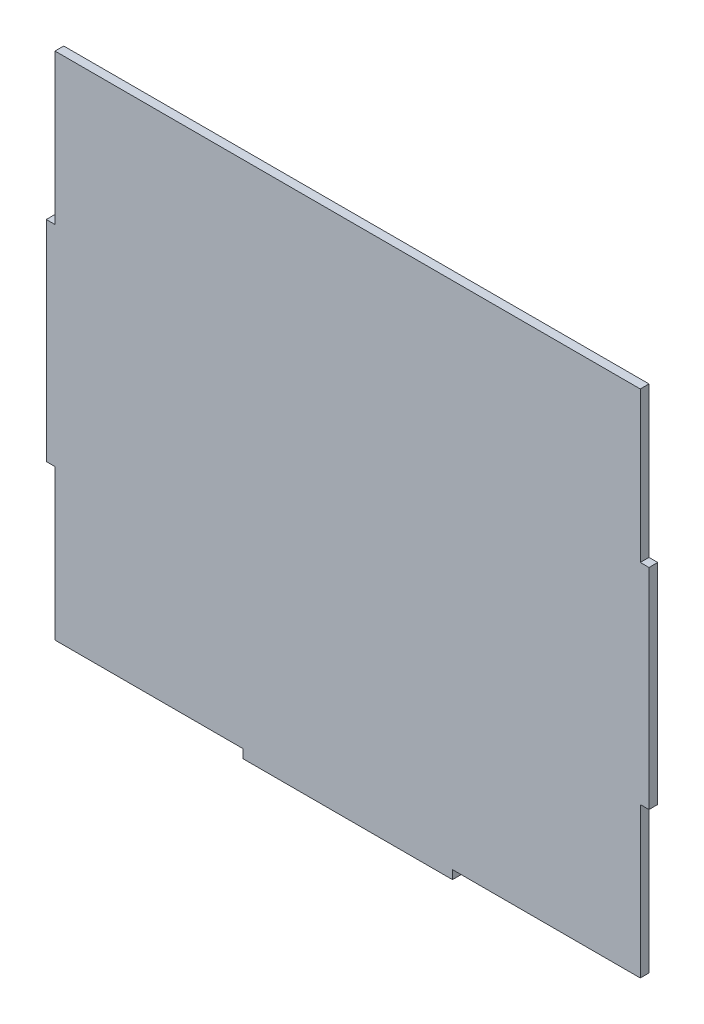
SolidWorks part; units mm, degrees
ref_plane "Front Plane" through (0, 0, 0) normal (0, 0, 1) x (1, 0, 0)
ref_plane "Top Plane" through (0, 0, 0) normal (0, 1, 0) x (1, 0, 0)
ref_plane "Right Plane" through (0, 0, 0) normal (1, 0, 0) x (0, 0, -1)
sketch "Sketch1" plane through (0, 0, 0) normal (0, 0, 1) x (1, 0, 0)
  line L1 (-106.3625, 92.71) -> (106.3625, 92.71)
  line L2 (-106.3625, 92.71) -> (-106.3625, -92.71)
  line L3 (-106.3625, -92.71) -> (106.3625, -92.71)
  line L4 (106.3625, 92.71) -> (106.3625, -92.71)
  line L5 (-106.3625, 92.71) -> (106.3625, -92.71) construction
  line L6 (-106.3625, -92.71) -> (106.3625, 92.71) construction
  point P0 (0, 0)
  dimension "D1" = 185.42
  dimension "D2" = 212.725
extrude "Boss-Extrude1" add sketch "Sketch1" along normal blind 3.175
sketch "Sketch2" plane through (0, 0, 3.175) normal (0, 0, 1) x (1, 0, 0)
  line L0 (-106.3625, 0) -> (-106.3625, 92.71) construction
  line L1 (-103.1875, -46.355) -> (-106.3625, -46.355) construction
  line L2 (-103.1875, -71.755) -> (-103.1875, -20.955)
  line L3 (-106.3625, 92.71) -> (-106.3625, -92.71) construction
  line L4 (-103.1875, 46.355) -> (-106.3625, 46.355) construction
  line L5 (-106.3625, 71.755) -> (-103.1875, 71.755)
  line L6 (-106.3625, 71.755) -> (-106.3625, 20.955)
  line L7 (-106.3625, 20.955) -> (-103.1875, 20.955)
  line L8 (-103.1875, 71.755) -> (-103.1875, 20.955)
  line L9 (-106.3625, 0) -> (0, 0) construction
  line L10 (-106.3625, -20.955) -> (-103.1875, -20.955)
  line L11 (-106.3625, -71.755) -> (-106.3625, -20.955)
  line L12 (-106.3625, -71.755) -> (-103.1875, -71.755)
  line L13 (0, 0) -> (0, 92.71) construction
  line L14 (106.3625, 92.71) -> (-106.3625, 92.71) construction
  line L15 (103.1875, 46.355) -> (106.3625, 46.355) construction
  line L16 (103.1875, -46.355) -> (106.3625, -46.355) construction
  line L17 (106.3625, -71.755) -> (103.1875, -71.755)
  line L18 (106.3625, -71.755) -> (106.3625, -20.955)
  line L19 (106.3625, -20.955) -> (103.1875, -20.955)
  line L20 (103.1875, 71.755) -> (103.1875, 20.955) construction
  line L21 (106.3625, 20.955) -> (103.1875, 20.955)
  line L22 (106.3625, 71.755) -> (106.3625, 20.955)
  line L23 (106.3625, 71.755) -> (103.1875, 71.755)
  line L24 (103.1875, -71.755) -> (103.1875, -20.955) construction
  line L25 (103.1875, -71.755) -> (100.0125, -71.755)
  line L26 (103.1875, 71.755) -> (100.0125, 71.755)
  line L27 (103.1875, 71.755) -> (103.1875, 20.955) construction
  line L28 (103.1875, 20.955) -> (100.0125, 20.955)
  line L29 (100.0125, 71.755) -> (100.0125, 20.955)
  line L30 (100.0125, -71.755) -> (100.0125, -20.955)
  line L31 (103.1875, -20.955) -> (100.0125, -20.955)
  dimension "D1" = 3.175
  dimension "D2" = 50.8
  dimension "D3" = 6.35
extrude "Cut-Extrude1" [suppressed] cut sketch "Sketch2" against normal through all
sketch "Sketch3" [suppressed] plane through (0, 0, 3.175) normal (0, 0, 1) x (1, 0, 0)
  line L0 (0, 114.3) -> (0, -114.3) construction
  line L1 (112.395, 114.3) -> (-112.395, 114.3) construction
  line L2 (-112.395, -114.3) -> (112.395, -114.3) construction
sketch "Sketch4" plane through (0, 0, 0) normal (0, 0, -1) x (-1, 0, 0)
  line L0 (106.3625, -92.71) -> (-106.3625, -92.71) construction
  line L1 (0, -89.535) -> (0, 92.71) construction
  line L2 (-38.1, -89.535) -> (38.1, -89.535)
  line L3 (-38.1, -89.535) -> (-38.1, -92.71)
  line L4 (-38.1, -92.71) -> (38.1, -92.71)
  line L5 (0, 0) -> (0, -92.71) construction
  line L6 (0, -92.71) -> (-106.3625, -92.71) construction
  line L7 (38.1, -89.535) -> (38.1, -92.71)
  line L9 (-106.3625, 92.71) -> (106.3625, 92.71) construction
  dimension "D1" = 76.2
  dimension "D2" = 3.175
extrude "Cut-Extrude2" [suppressed] cut sketch "Sketch4" against normal through all
sketch "Sketch5" plane through (0, 0, 0) normal (0, 0, -1) x (-1, 0, 0)
  line L0 (-106.3625, 0) -> (0, 0) construction
  line L1 (-106.3625, 38.1) -> (-109.5375, 38.1)
  line L2 (-106.3625, 38.1) -> (-106.3625, -38.1)
  line L3 (-106.3625, -38.1) -> (-109.5375, -38.1)
  line L4 (-109.5375, 38.1) -> (-109.5375, -38.1)
  line L5 (-106.3625, 38.1) -> (-109.5375, -38.1) construction
  line L6 (-106.3625, -38.1) -> (-109.5375, 38.1) construction
  line L7 (-106.3625, -92.71) -> (-106.3625, 92.71) construction
  line L8 (0, 0) -> (0, 92.71) construction
  line L9 (-106.3625, 92.71) -> (106.3625, 92.71) construction
  line L10 (106.3625, -38.1) -> (109.5375, 38.1) construction
  line L11 (106.3625, 38.1) -> (109.5375, -38.1) construction
  line L12 (109.5375, 38.1) -> (109.5375, -38.1)
  line L13 (106.3625, -38.1) -> (109.5375, -38.1)
  line L14 (106.3625, 38.1) -> (106.3625, -38.1)
  line L15 (106.3625, 38.1) -> (109.5375, 38.1)
  point P0 (-107.95, 0)
  point P17 (107.95, 0)
  dimension "D1" = 76.2
  dimension "D2" = 3.175
extrude "Boss-Extrude2" add sketch "Sketch5" against normal up to surface (3.175 mm away) up to face at (0, 0, 3.175)
sketch "Sketch6" plane through (0, 0, 0) normal (0, 0, -1) x (-1, 0, 0)
  line L0 (106.3625, -92.71) -> (-106.3625, -92.71) construction
  line L1 (0, 8.89) -> (0, 92.71) construction
  line L2 (-106.3625, 92.71) -> (106.3625, 92.71) construction
  line B0 (-38.1, -95.885) -> (-38.1, -92.71)
  line B1 (-38.1, -95.885) -> (38.1, -95.885)
  line B2 (38.1, -95.885) -> (38.1, -92.71)
  line B3 (-38.1, -92.71) -> (38.1, -92.71)
sketch_block_instance "Block-tabsSideWallsToBack-1"
sketch_block "Block-tabsSideWallsToBack"
extrude "Boss-Extrude3" add sketch "Sketch6" against normal up to surface (3.175 mm away) up to face at (0, 0, 3.175)
equation "\"flipWidth\"= 6.5"
equation "\"flipHeight\"= 4"
equation "\"spindleLength\"= 7.75"
equation "\"bearingID\"= 0.1559"
equation "\"motorWidth\"= 0.79"
equation "\"motorHeight\"= 1.0"
equation "\"motorLength\"= 1.58"
equation "\"spindleMaxDiam\"= 2.75"
equation "\"D1@Sketch1\"=\"depth\""
equation "\"totalLength\"= 15"
equation "\"depth\"= 7.3"
equation "\"height\"= 9.5"
equation "\"bearingOD\"= 0.3539\t"
equation "\"width\"= 8.50"
equation "\"D2@Sketch1\"=\"width\"- 1/8"
